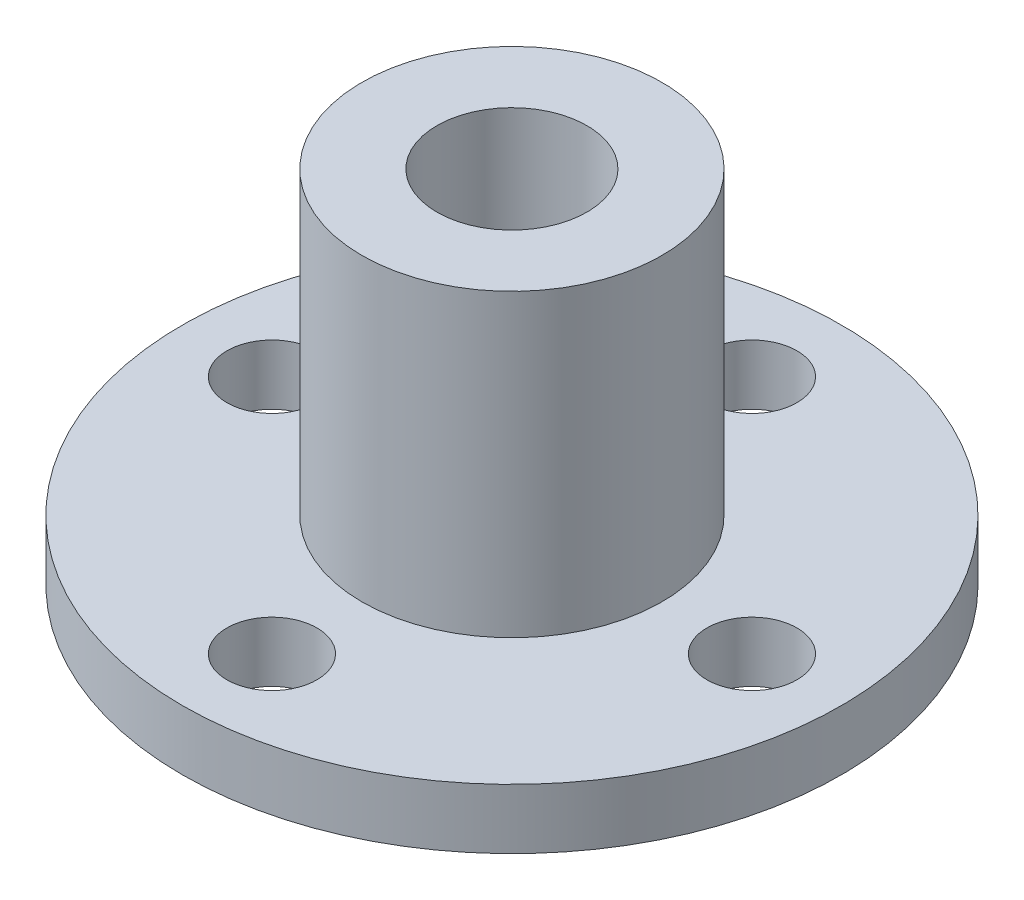
SolidWorks part; units mm, degrees
ref_plane "Front Plane" through (0, 0, 0) normal (0, 0, 1) x (1, 0, 0)
ref_plane "Top Plane" through (0, 0, 0) normal (0, 1, 0) x (1, 0, 0)
ref_plane "Right Plane" through (0, 0, 0) normal (1, 0, 0) x (0, 0, -1)
sketch "Sketch1" plane through (0, 0, 0) normal (0, 1, 0) x (1, 0, 0)
  circle A0 centre (0, 0) radius 10.9855
  dimension "D1" = 21.971
extrude "Boss-Extrude1" add sketch "Sketch1" along normal blind 2
sketch "Sketch3" plane through (0, 2, 0) normal (0, 1, 0) x (1, 0, 0)
  circle A0 centre (0, 0) radius 5
  dimension "D1" = 10
extrude "Boss-Extrude2" add sketch "Sketch3" along normal blind 10
sketch "Sketch2" plane through (0, 2, 0) normal (0, 1, 0) x (1, 0, 0)
  circle A0 centre (0, 0) radius 2.5
  dimension "D1" = 5
extrude "Cut-Extrude1" cut sketch "Sketch2" against normal through all both and the other way through all
sketch "Sketch4" plane through (0, 2, 0) normal (0, 1, 0) x (1, 0, 0)
  line L0 (0, -8) -> (0, 8) construction
  line L1 (-8, 0) -> (8, 0) construction
  circle A0 centre (8, 0) radius 1.5
  circle A1 centre (0, -8) radius 1.5
  circle A2 centre (-8, 0) radius 1.5
  circle A3 centre (0, 8) radius 1.5
  dimension "D3" = 3
  dimension "D4" = 3
  dimension "D5" = 3
  dimension "D6" = 3
  dimension "D1" = 16
  dimension "D2" = 16
extrude "Cut-Extrude2" cut sketch "Sketch4" against normal blind 10
equation "\"D4@Sketch4\"=\"D3@Sketch4\""
equation "\"D5@Sketch4\"=\"D3@Sketch4\""
equation "\"D6@Sketch4\"=\"D3@Sketch4\""
